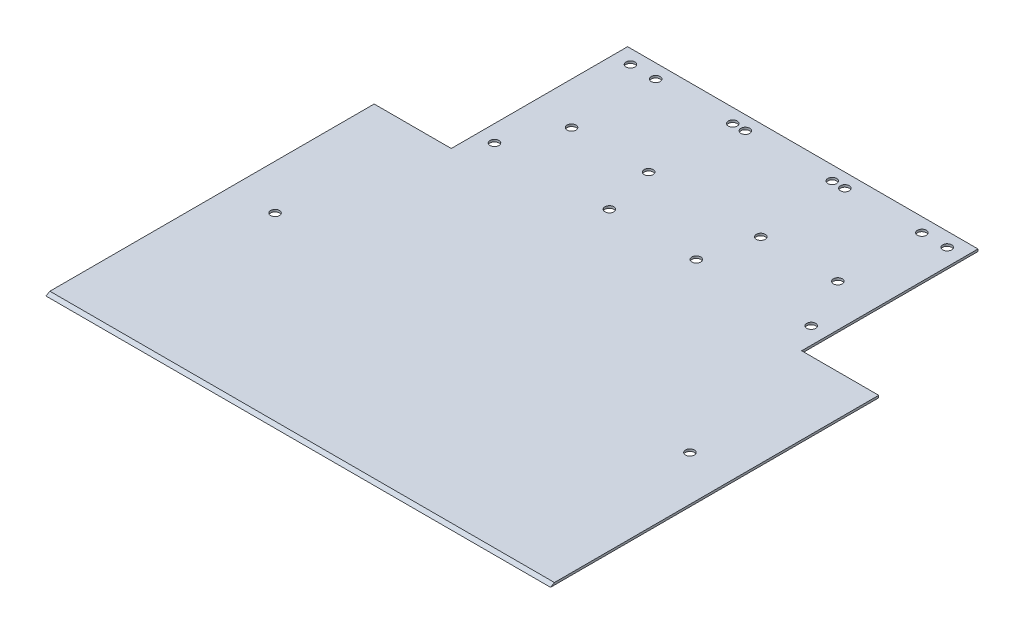
SolidWorks part; units mm, degrees
ref_plane "Alzado" through (0, 0, 0) normal (0, 0, 1) x (1, 0, 0)
ref_plane "Planta" through (0, 0, 0) normal (0, 1, 0) x (1, 0, 0)
ref_plane "Vista lateral" through (0, 0, 0) normal (1, 0, 0) x (0, 0, -1)
sketch "Croquis1" plane through (0, 0, 0) normal (0, 1, 0) x (1, 0, 0)
  line L0 (-62.5, 90) -> (-62.5, 27.08)
  line L1 (90, -90) -> (-90, -90)
  line L2 (90, -90) -> (90, 27.08)
  line L3 (62.5, 90) -> (-62.5, 90)
  line L4 (-90, -90) -> (-90, 27.08)
  line L5 (90, -90) -> (-62.5, 62.5) construction
  line L6 (62.5, 62.5) -> (-90, -90) construction
  line L7 (-62.5, 27.08) -> (-90, 27.08)
  line L8 (0, 90) -> (0, -90) construction
  line L9 (62.5, 27.08) -> (90, 27.08)
  line L10 (62.5, 90) -> (62.5, 27.08)
  point P0 (0, 0)
  dimension "D1" = 125
  dimension "D2" = 180
  dimension "D3" = 27.5
  dimension "D4" = 62.92
  dimension "D5" = 27.5
extrude "Saliente-Extruir1" add sketch "Croquis1" along normal blind 0.8
sketch "Croquis2" plane through (-90, 0, 0) normal (-1, 0, 0) x (0, 0, 1)
  line L0 (90, 0) -> (88.6144, 0.8)
  line L1 (-27.08, 0.8) -> (90, 0.8) construction
  line L2 (88.6144, 0.8) -> (90, 0.8)
  line L3 (90, 0.8) -> (90, 0)
  dimension "D1" = 60
extrude "Cortar-Extruir1" cut sketch "Croquis2" against normal up to next
sketch "Croquis3" plane through (0, 0.8, 0) normal (0, 1, 0) x (1, 0, 0)
  circle A0 centre (74, -24.2793) radius 1.585
extrude "Cortar-Extruir2" cut sketch "Croquis3" against normal up to next (0.8 mm away)
mirror "Simetría1" about plane through (0, 0, 0) normal (1, 0, 0) of "Cortar-Extruir2"
sketch "Croquis4" plane through (0, 0.8, 0) normal (0, 1, 0) x (1, 0, 0)
  circle A0 centre (-56.5, 36.5056) radius 1.585
  circle A1 centre (-15.5, 36.5056) radius 1.585
  circle A2 centre (-15.5, 85.0056) radius 1.585
  circle A3 centre (-56.5, 85.0056) radius 1.585
extrude "Cortar-Extruir3" cut sketch "Croquis4" against normal up to next
sketch "Croquis6" plane through (0, 0.8, 0) normal (0, 1, 0) x (1, 0, 0)
  circle A0 centre (56.5, 85.0056) radius 1.585
  circle A1 centre (15.5, 85.0056) radius 1.585
  circle A2 centre (15.5, 36.5056) radius 1.585
  circle A3 centre (56.5, 36.5056) radius 1.585
extrude "Cortar-Extruir4" cut sketch "Croquis6" against normal up to next
sketch "Croquis7" plane through (0, 0.8, 0) normal (0, 1, 0) x (1, 0, 0)
  circle A0 centre (-20, 85.0056) radius 1.585
  circle A1 centre (-47.5, 85.0056) radius 1.585
  circle A2 centre (-47.5, 55.0056) radius 1.585
  circle A3 centre (-20, 55.0056) radius 1.585
extrude "Cortar-Extruir5" cut sketch "Croquis7" against normal up to next (0.8 mm away)
mirror "Simetría2" about plane through (0, 0, 0) normal (1, 0, 0) of "Cortar-Extruir5"
